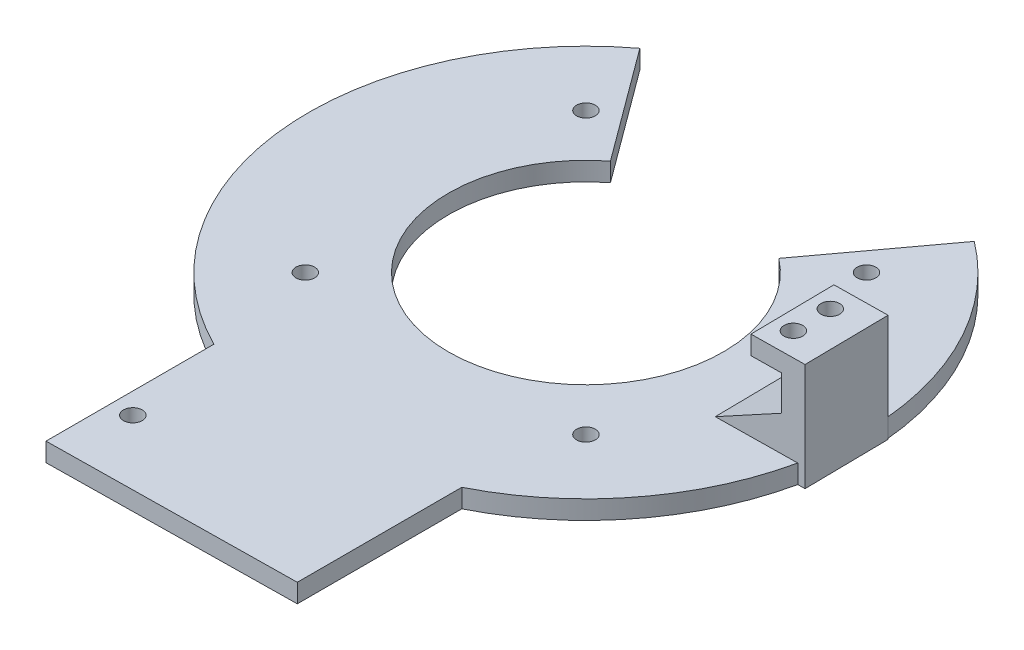
SolidWorks part; units mm, degrees
ref_plane "Front Plane" through (0, 0, 0) normal (0, 0, 1) x (1, 0, 0)
ref_plane "Top Plane" through (0, 0, 0) normal (0, 1, 0) x (1, 0, 0)
ref_plane "Right Plane" through (0, 0, 0) normal (1, 0, 0) x (0, 0, -1)
sketch "Sketch1" plane through (0, 0, 0) normal (0, 1, 0) x (1, 0, 0)
  line L0 (-18, 23.2456) -> (-35.75, 47.287)
  line L1 (18, 23.2456) -> (35.75, 47.287)
  line L2 (-26.5, -53.0271) -> (-26.5, -88.9371)
  line L5 (0, 0) -> (0, -88.5708) construction
  line L6 (-18, 23.2456) -> (18, 23.2456) construction
  line L7 (-35.75, 47.287) -> (35.75, 47.287) construction
  line L9 (26.5, -53.0271) -> (26.5, -88.2046)
  line L11 (26.5, -88.2046) -> (-26.5, -88.9371)
  arc A0 (-35.75, 47.287) -> (-26.5, -53.0271) centre (0, 0) ccw
  arc A1 (-18, 23.2456) -> (18, 23.2456) centre (0, 0) ccw
  arc A2 (26.5, -53.0271) -> (35.75, 47.287) centre (0, 0) ccw
  circle A3 centre (-22, -74.8735) radius 2
  dimension "D3" = 29.4
  dimension "D4" = 59.28
  dimension "D7" = 4
  dimension "D1" = 36
  dimension "D2" = 71.5
  dimension "D5" = 35.91
  dimension "D6" = 53
  dimension "D8" = 14
  dimension "D9" = 4.5
extrude "Boss-Extrude1" add sketch "Sketch1" along normal blind 4
sketch "Sketch13" plane through (0, 4, 0) normal (0, 1, 0) x (1, 0, 0)
  line L0 (30, 30) -> (-30, -30) construction
  line L1 (30, 30) -> (-30, 30)
  line L2 (30, 30) -> (30, -30)
  line L3 (30, -30) -> (-30, -30)
  line L4 (-30, 30) -> (-30, -30)
  line L5 (30, -30) -> (-30, 30) construction
  point P4 (0, 0)
  point P5 (-21.7976, 21.7976)
  point P7 (-21.7976, 21.7976)
  point P9 (-30, 30)
  dimension "D1" = 60
  dimension "D2" = 60
  dimension "D3" = 11.6
hole_wizard "Ø4.0mm Dowel Slot1" positions "Sketch14" profile "Sketch15" size "Ø4.0" standard "BSI" slot yes
sketch "Sketch14" plane through (0, 4, 0) normal (0, 1, 0) x (1, 0, 0)
  point P0 (30, 30)
  point P3 (30, -30)
  point P6 (-30, -30)
  point P9 (-30, 30)
sketch "Sketch15" plane through (30, 4, -30) normal (1, 0, 0) x (0, 0, 1)
  line L0 (0, 0) -> (0, 11.3017)
  line L1 (0, 11.3017) -> (2, 10.1)
  line L2 (2, 10.1) -> (2, 0)
  line L5 (2, 0) -> (0, 0)
  line L10 (0, 11.3017) -> (-2, 10.1) construction
  line L11 (0, -6.35) -> (0, 107.95) construction
  dimension "Hole Dia." = 4
  dimension "Hole Depth" = 10.1
  dimension "Drill Angle" = 118
ref_plane "Plane1" through (0.1855, 0, 13.4211) normal (0.0138, 0, 0.9999) x (0.9999, 0, -0.0138)
sketch "Sketch16" plane through (0.1855, 0, 13.4211) normal (0.0138, 0, 0.9999) x (0.9999, 0, -0.0138)
  line L0 (54.4273, 0) -> (59.28, 0)
  line L1 (59.28, 0) -> (59.28, 23)
  line L2 (59.28, 23) -> (47.86, 23)
  line L3 (47.86, 23) -> (47.86, 19)
  line L4 (47.86, 19) -> (54.28, 19)
  line L5 (54.28, 19) -> (54.28, 4)
  line L6 (54.28, 4) -> (54.4273, 4)
  line L7 (54.4273, 4) -> (54.4273, 0)
  line L8 (55.2583, 4) -> (55.2583, 25.7631) construction
  dimension "D1" = 4
  dimension "D2" = 5
  dimension "D3" = 4
  dimension "D5" = 23
  dimension "D6" = 11.42
extrude "Boss-Extrude2" add sketch "Sketch16" against normal blind 18
ref_plane "Plane2" through (0.0611, 0, 4.4219) normal (0.0138, 0, 0.9999) x (0.9999, 0, -0.0138)
sketch "Sketch17" plane through (0.0611, 0, 4.4219) normal (0.0138, 0, 0.9999) x (0.9999, 0, -0.0138)
  line L1 (54.28, 11.5119) -> (40.3403, 4)
  line L2 (57.7404, 4) -> (25.7647, 4) construction
  line L3 (54.28, 19) -> (54.28, 4) construction
rib "Rib3" sketch "Sketch17" sketch "Sketch17" thickness 18 extrusion direction parallel to sketch draft on no parameters "D1"=18
sketch "Sketch18" plane through (0, 23, 0) normal (0, 1, 0) x (1, 0, 0)
  line L0 (51.97, -7.6027) -> (51.8595, 0.3973) construction
  line L1 (47.7922, 5.2386) -> (48.0409, -12.7597) construction
  line L2 (51.9147, -3.6027) -> (59.3355, -3.6027) construction
  line L3 (59.2111, 5.3964) -> (59.4598, -12.6018) construction
  point P8 (47.9165, -3.7605)
  dimension "D1" = 8
  dimension "D2" = 4
hole_wizard "Ø4.0mm Dowel Hole1" positions "Sketch19" profile "Sketch20" hole size "Ø4.0" standard "ISO" end condition up to next
sketch "Sketch19" plane through (0, 23, 0) normal (0, 1, 0) x (1, 0, 0)
  point P0 (51.97, -7.6027)
  point P3 (51.8595, 0.3973)
sketch "Sketch20" plane through (51.97, 23, 7.6027) normal (1, 0, 0) x (0, 0, 1)
  line L0 (0, 0) -> (0, 4)
  line L1 (0, 4) -> (2, 4)
  line L2 (2, 4) -> (2, 0)
  line L5 (2, 0) -> (0, 0)
  line L11 (0, -6.35) -> (0, 107.95) construction
  dimension "Thru Hole Dia." = 4
  dimension "Thru Hole Depth" = 4
